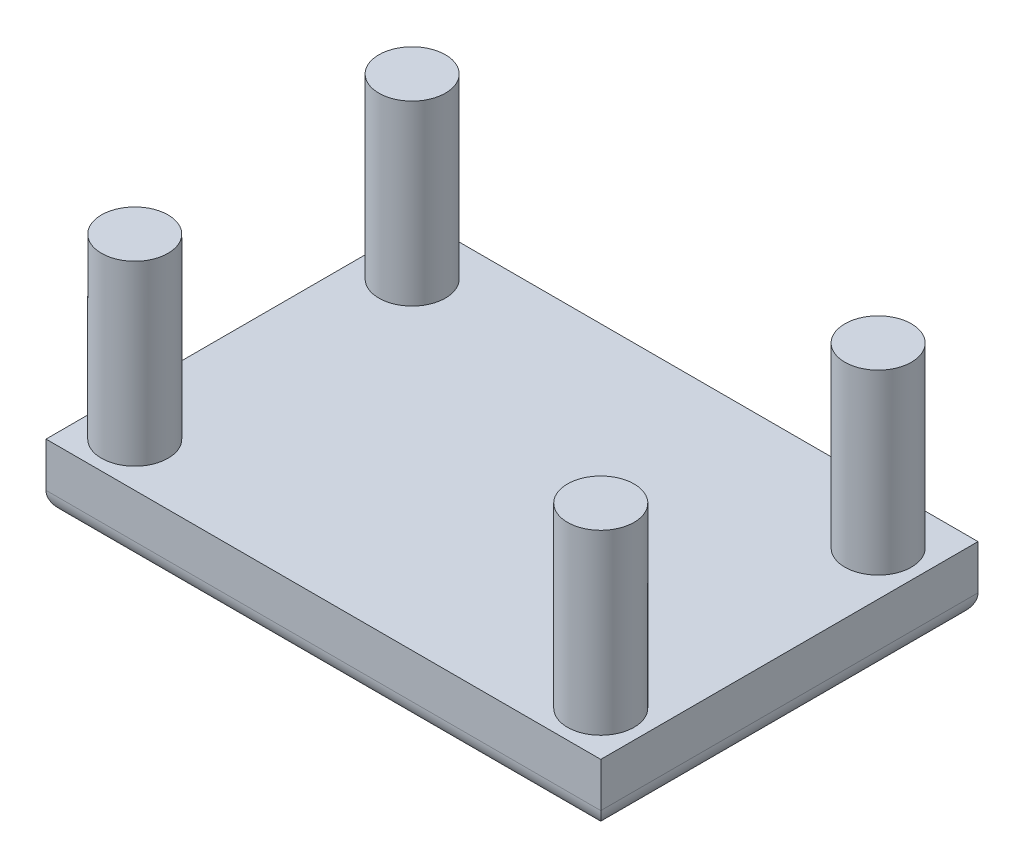
SolidWorks part; units mm, degrees
ref_plane "Front Plane" through (0, 0, 0) normal (0, 0, 1) x (1, 0, 0)
ref_plane "Top Plane" through (0, 0, 0) normal (0, 1, 0) x (1, 0, 0)
ref_plane "Right Plane" through (0, 0, 0) normal (1, 0, 0) x (0, 0, -1)
sketch "Sketch1" plane through (0, 0, 0) normal (0, 1, 0) x (1, 0, 0)
  line L1 (-12.5, -8.5) -> (12.5, -8.5)
  line L2 (-12.5, -8.5) -> (-12.5, 8.5)
  line L3 (-12.5, 8.5) -> (12.5, 8.5)
  line L4 (12.5, -8.5) -> (12.5, 8.5)
  line L5 (-12.5, -8.5) -> (12.5, 8.5) construction
  line L6 (-12.5, 8.5) -> (12.5, -8.5) construction
  point P0 (0, 0)
  dimension "D1" = 25
  dimension "D2" = 17
extrude "Boss-Extrude1" add sketch "Sketch1" along normal blind 3
sketch "Sketch2" plane through (0, 3, 0) normal (0, 1, 0) x (1, 0, 0)
  circle A0 centre (-10.5, -6.5) radius 1.5
  circle A1 centre (10.5, -6.5) radius 1.5
  circle A2 centre (10.5, 6) radius 1.5
  circle A3 centre (-10.5, 6) radius 1.5
extrude "Boss-Extrude2" add sketch "Sketch2" along normal blind 8
fillet "Fillet3" radius 1 4 edges at (0, 0, -8.5) (-12.5, 0, 0) (0, 0, 8.5) (12.5, 0, 0)
